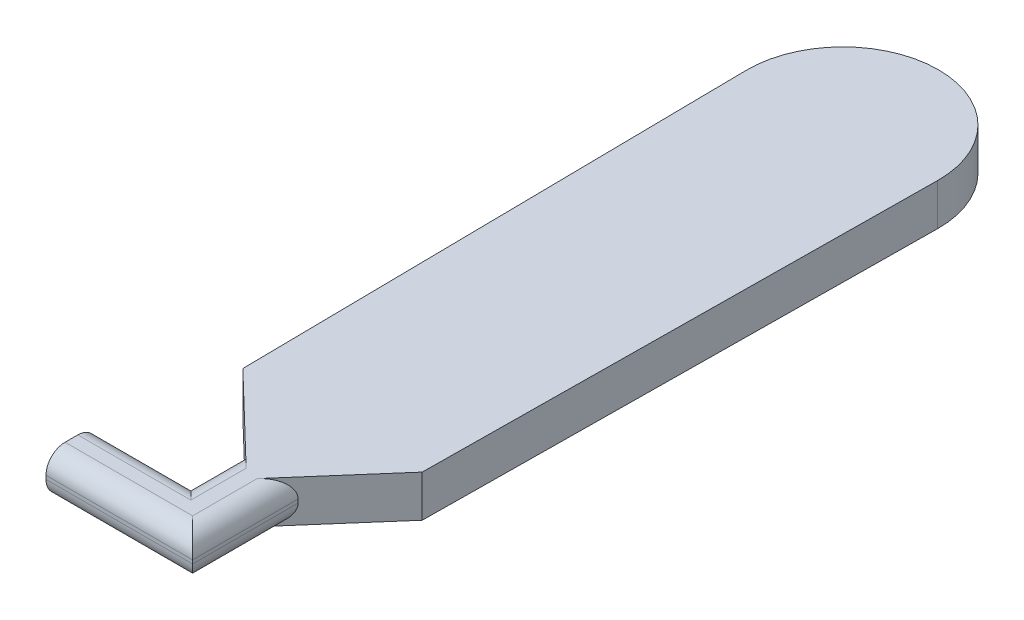
SolidWorks part; units mm, degrees
ref_plane "Front Plane" through (0, 0, 0) normal (0, 0, 1) x (1, 0, 0)
ref_plane "Top Plane" through (0, 0, 0) normal (0, 1, 0) x (1, 0, 0)
ref_plane "Right Plane" through (0, 0, 0) normal (1, 0, 0) x (0, 0, -1)
sketch "Sketch2" plane through (0, 0, 0) normal (0, 1, 0) x (1, 0, 0)
  line L0 (-4.4522, 98.0892) -> (96.0743, 98.0892) construction
  line L1 (7.673, 77.7507) -> (6.0346, 204.9371)
  line L2 (51.9756, 204.9371) -> (50.6772, 77.7507)
  line L3 (7.673, 77.7507) -> (24.1924, 61.8552)
  line L4 (24.1924, 61.8552) -> (36.8166, 61.8552)
  line L5 (36.8166, 61.8552) -> (50.6772, 77.7507)
  line L6 (24.1924, 61.8552) -> (24.1924, 48.7663)
  line L7 (24.1924, 48.7663) -> (1.6729, 48.7663)
  line L8 (1.6729, 48.7663) -> (1.6729, 36.5646)
  line L9 (1.6729, 36.5646) -> (36.8166, 36.5646)
  line L10 (36.8166, 36.5646) -> (36.8166, 61.8552)
  circle A0 centre (29.0117, 200.2428) radius 22.9148
extrude "Boss-Extrude1" add sketch "Sketch2" along normal blind 10 contours L1 L0 L2 A0 | A0 | L0 L1 L3 L4 L5 L2 | L9 L10 L4 L6 L7 L8
fillet "Fillet1" radius 4.572 8 edges at (19.2448, 0, -36.5646) (19.2448, 10, -36.5646) (36.8166, 0, -49.2099) (36.8166, 10, -49.2099) (24.1924, 0, -55.3108) (24.1924, 10, -55.3108) (12.9327, 0, -48.7663) (12.9327, 10, -48.7663)
